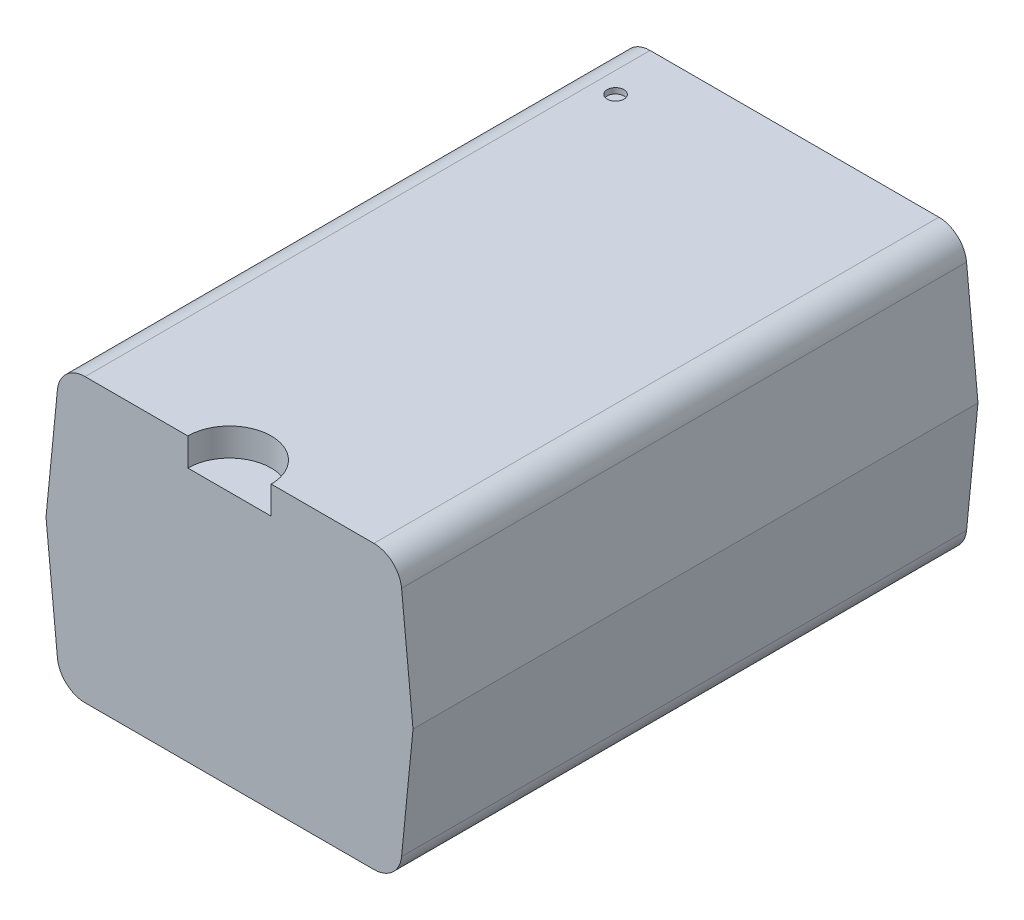
SolidWorks part; units mm, degrees
ref_plane "Front Plane" through (0, 0, 0) normal (0, 0, 1) x (1, 0, 0)
ref_plane "Top Plane" through (0, 0, 0) normal (0, 1, 0) x (1, 0, 0)
ref_plane "Right Plane" through (0, 0, 0) normal (1, 0, 0) x (0, 0, -1)
sketch "Sketch1" plane through (0, 0, 0) normal (0, 0, 1) x (1, 0, 0)
  line L0 (-33.7892, 21.1912) -> (-27.6892, 21.1912)
  line L1 (-42.1718, 18.6512) -> (-9.2641, 18.6512) construction
  line L2 (-33.7892, 16.1112) -> (-27.6892, 16.1112)
  line L3 (-33.7892, 16.1112) -> (-34.0392, 18.6512)
  line L4 (-30.7392, 24.6276) -> (-30.7392, 10.8537) construction
  line L5 (-27.6892, 16.1112) -> (-27.4392, 18.6512)
  line L6 (-33.7892, 21.1912) -> (-34.0392, 18.6512)
  line L7 (-27.6892, 21.1912) -> (-27.4392, 18.6512)
  dimension "D1" = 6.1
  dimension "D2" = 18.6512
  dimension "D3" = 2.54
  dimension "D5" = 3.05
extrude "Boss-Extrude1" add sketch "Sketch1" along normal blind 10.16
fillet "Fillet1" radius 0.5 4 edges at (-27.6892, 16.1112, 5.08) (-33.7892, 16.1112, 5.08) (-33.7892, 21.1912, 5.08) (-27.6892, 21.1912, 5.08)
ref_plane "Plane2" through (-36.5259, 3.5951, 0) normal (-0.9952, 0.098, 0) x (0, 0, 1)
sketch "Sketch5" plane through (-36.5259, 3.5951, 0) normal (-0.9952, 0.098, 0) x (0, 0, 1)
  line L0 (5.08, 18.3327) -> (5.08, 7.3108) construction
  line L1 (10.16, 18.3327) -> (0, 18.3327) construction
  line L2 (0.57, 16.2975) -> (9.59, 16.2975) construction
  line L3 (0.57, 16.2975) -> (0.57, 19.9846) construction
  line L4 (9.59, 16.2975) -> (9.59, 19.9846) construction
  point P6 (5.08, 16.2975)
  dimension "D1" = 9.02
  dimension "D2" = 0
ref_plane "Plane3" through (0, 31.1912, 0) normal (0, 1, 0) x (1, 0, 0)
sketch "Sketch36" plane through (0, 21.1912, 0) normal (0, 1, 0) x (1, 0, 0)
  circle A0 centre (-32.962, -0.9949) radius 0.15
  dimension "D1" = 0.3
extrude "Cut-Extrude26" cut sketch "Sketch36" against normal blind 0.1
sketch "Sketch37" plane through (0, 21.1912, 0) normal (0, 1, 0) x (1, 0, 0)
  line L0 (-28.1424, -10.16) -> (-33.336, -10.16) construction
  circle A0 centre (-30.7392, -10.16) radius 0.75
  dimension "D1" = 1.5
extrude "Cut-Extrude27" cut sketch "Sketch37" against normal blind 0.5
